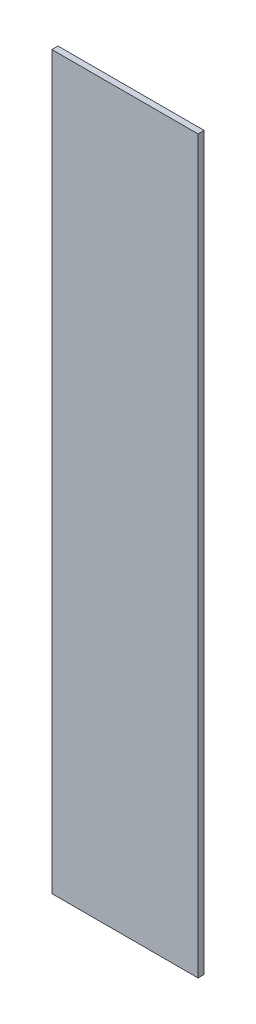
SolidWorks part; units mm, degrees
material "7075-O (SS)"
ref_plane "Front Plane" through (0, 0, 0) normal (0, 0, 1) x (1, 0, 0)
ref_plane "Top Plane" through (0, 0, 0) normal (0, 1, 0) x (1, 0, 0)
ref_plane "Right Plane" through (0, 0, 0) normal (1, 0, 0) x (0, 0, -1)
sketch "Sketch1" plane through (0, 0, 0) normal (0, 0, 1) x (1, 0, 0)
  line L1 (-60, -300) -> (60, -300)
  line L2 (-60, -300) -> (-60, 300)
  line L3 (-60, 300) -> (60, 300)
  line L4 (60, -300) -> (60, 300)
  line L5 (-60, -300) -> (60, 300) construction
  line L6 (-60, 300) -> (60, -300) construction
  point P0 (0, 0)
  dimension "D1" = 600
  dimension "D2" = 120
extrude "Boss-Extrude1" add sketch "Sketch1" along normal blind 5
